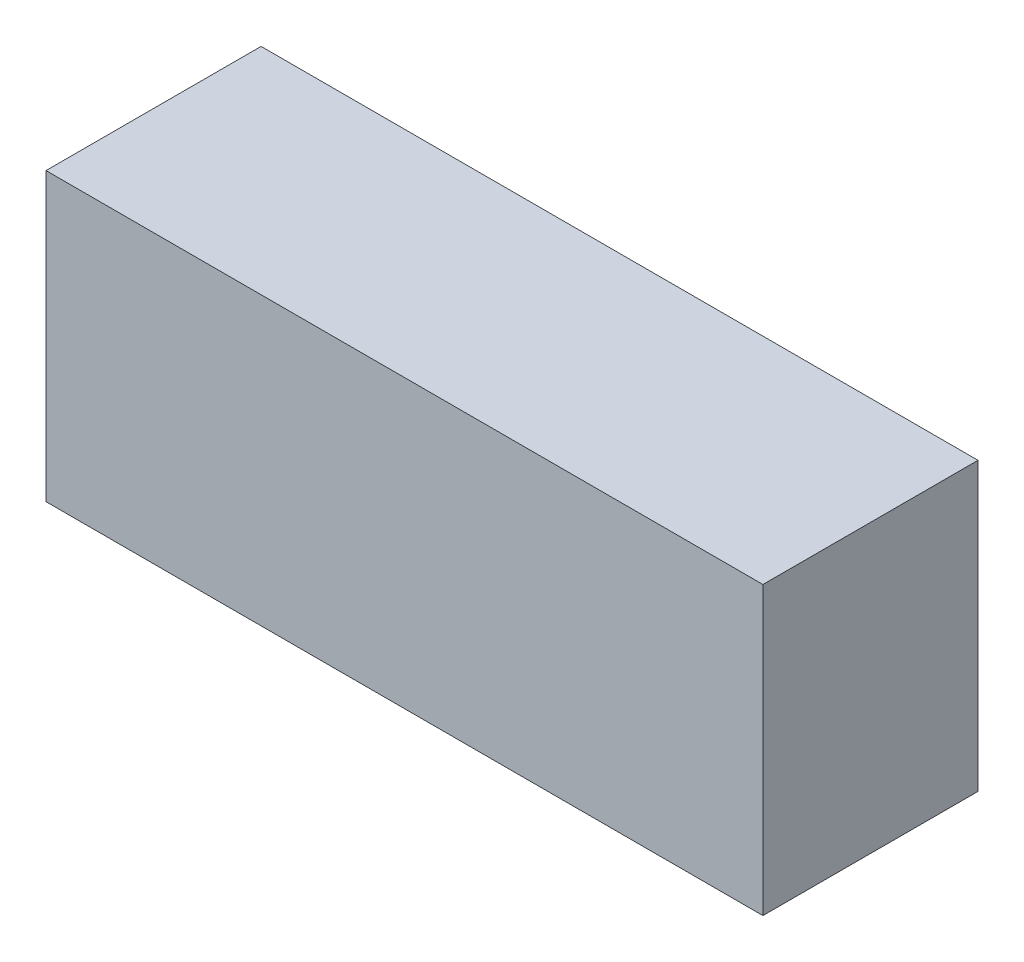
SolidWorks part; units mm, degrees
ref_plane "Front Plane" through (0, 0, 0) normal (0, 0, 1) x (1, 0, 0)
ref_plane "Top Plane" through (0, 0, 0) normal (0, 1, 0) x (1, 0, 0)
ref_plane "Right Plane" through (0, 0, 0) normal (1, 0, 0) x (0, 0, -1)
sketch "Sketch1" plane through (0, 0, 0) normal (0, 0, 1) x (1, 0, 0)
  line L1 (0, 0) -> (-10, 0)
  line L2 (0, 0) -> (0, -4)
  line L3 (0, -4) -> (-10, -4)
  line L4 (-10, 0) -> (-10, -4)
  dimension "D1" = 10
  dimension "D2" = 4
extrude "Boss-Extrude1" add sketch "Sketch1" along normal blind 3
